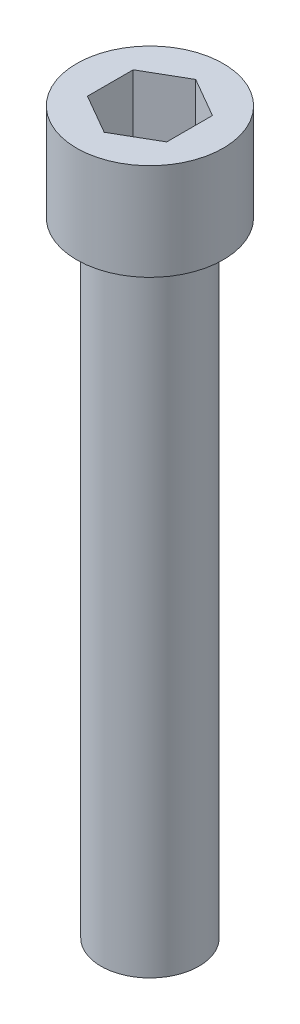
SolidWorks part; units mm, degrees
ref_plane "Front Plane" through (0, 0, 0) normal (0, 0, 1) x (1, 0, 0)
ref_plane "Top Plane" through (0, 0, 0) normal (0, 1, 0) x (1, 0, 0)
ref_plane "Right Plane" through (0, 0, 0) normal (1, 0, 0) x (0, 0, -1)
sketch "Sketch1" plane through (0, 0, 0) normal (0, 1, 0) x (1, 0, 0)
  circle A0 centre (0, 0) radius 5.875
  dimension "D1" = 11.75
extrude "Boss-Extrude1" add sketch "Sketch1" along normal blind 7.75
sketch "Sketch2" plane through (0, 7.75, 0) normal (0, 1, 0) x (1, 0, 0)
  line L1 (0, 3.6662) -> (-3.175, 1.8331)
  line L2 (-3.175, 1.8331) -> (-3.175, -1.8331)
  line L3 (-3.175, -1.8331) -> (0, -3.6662)
  line L4 (0, -3.6662) -> (3.175, -1.8331)
  line L5 (3.175, -1.8331) -> (3.175, 1.8331)
  line L6 (3.175, 1.8331) -> (0, 3.6662)
  circle A0 centre (0, 0) radius 3.175 construction
  dimension "D1" = 6.35
extrude "Cut-Extrude1" cut sketch "Sketch2" against normal blind 5.5
sketch "Sketch3" plane through (0, 0, 0) normal (0, -1, 0) x (1, 0, 0)
  circle A0 centre (0, 0) radius 3.925
  dimension "D1" = 7.85
extrude "Boss-Extrude2" add sketch "Sketch3" along normal blind 10
sketch "Sketch4" plane through (0, -10, 0) normal (0, -1, 0) x (1, 0, 0)
  circle A0 centre (0, 0) radius 3.925
  dimension "D1" = 7.85
extrude "Boss-Extrude3" add sketch "Sketch4" along normal blind 40
